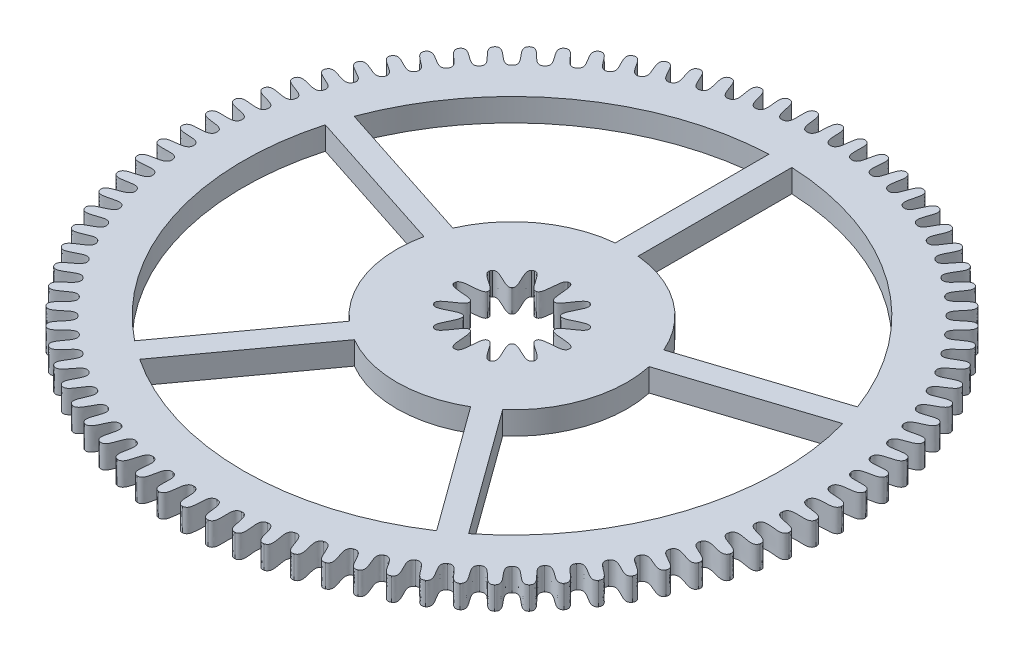
SolidWorks part; units mm, degrees
ref_plane "Alzado" through (0, 0, 0) normal (0, 0, 1) x (1, 0, 0)
ref_plane "Planta" through (0, 0, 0) normal (0, 1, 0) x (1, 0, 0)
ref_plane "Vista lateral" through (0, 0, 0) normal (1, 0, 0) x (0, 0, -1)
sketch "Sketch1" plane through (0, 0, 0) normal (0, 1, 0) x (1, 0, 0)
  line L0 (0, -1000) -> (0, 49000) construction
  line L1 (0, 0) -> (1869.5597, 49965.0352) construction
  circle A0 centre (0, 0) radius 4.315 construction
  circle A1 centre (0, 0) radius 4.015 construction
  spline S0 degree 3 poles (0, 4.315) (0.1353, 4.3129) (0.008, 4.0167) (0.1501, 4.0122) knots 0 0 0 0 1 1 1 1
  spline S1 degree 3 poles (0, 4.315) (-0.1353, 4.3129) (-0.008, 4.0167) (-0.1501, 4.0122) knots 0 0 0 0 1 1 1 1
  spline S2 degree 3 poles (0.3225, 4.3029) (0.4572, 4.2907) (0.3081, 4.0048) (0.4495, 3.9898) knots 0 0 0 0 1 1 1 1
  spline S3 degree 3 poles (0.3225, 4.3029) (0.1874, 4.3109) (0.2922, 4.006) (0.1501, 4.0122) knots 0 0 0 0 1 1 1 1
  spline S4 degree 3 poles (0.6431, 4.2668) (0.7765, 4.2445) (0.6066, 3.9706) (0.7464, 3.945) knots 0 0 0 0 1 1 1 1
  spline S5 degree 3 poles (0.6431, 4.2668) (0.5091, 4.2849) (0.5907, 3.973) (0.4495, 3.9898) knots 0 0 0 0 1 1 1 1
  spline S6 degree 3 poles (0.9602, 4.2068) (1.0916, 4.1746) (0.9016, 3.9142) (1.0392, 3.8782) knots 0 0 0 0 1 1 1 1
  spline S7 degree 3 poles (0.9602, 4.2068) (0.8278, 4.2348) (0.886, 3.9177) (0.7464, 3.945) knots 0 0 0 0 1 1 1 1
  spline S8 degree 3 poles (1.2719, 4.1233) (1.4005, 4.0814) (1.1916, 3.8358) (1.3261, 3.7897) knots 0 0 0 0 1 1 1 1
  spline S9 degree 3 poles (1.2719, 4.1233) (1.142, 4.1611) (1.1763, 3.8406) (1.0392, 3.8782) knots 0 0 0 0 1 1 1 1
  spline S10 degree 3 poles (1.5764, 4.0167) (1.7016, 3.9653) (1.4749, 3.7361) (1.6056, 3.68) knots 0 0 0 0 1 1 1 1
  spline S11 degree 3 poles (1.5764, 4.0167) (1.4498, 4.0642) (1.46, 3.7419) (1.3261, 3.7897) knots 0 0 0 0 1 1 1 1
  spline S12 degree 3 poles (1.8722, 3.8877) (1.9932, 3.8271) (1.75, 3.6154) (1.8761, 3.5497) knots 0 0 0 0 1 1 1 1
  spline S13 degree 3 poles (1.8722, 3.8877) (1.7494, 3.9445) (1.7356, 3.6223) (1.6056, 3.68) knots 0 0 0 0 1 1 1 1
  spline S14 degree 3 poles (2.1575, 3.7369) (2.2736, 3.6674) (2.0153, 3.4745) (2.1361, 3.3996) knots 0 0 0 0 1 1 1 1
  spline S15 degree 3 poles (2.1575, 3.7369) (2.0393, 3.8027) (2.0014, 3.4825) (1.8761, 3.5497) knots 0 0 0 0 1 1 1 1
  spline S16 degree 3 poles (2.4307, 3.5652) (2.5413, 3.4873) (2.2693, 3.3142) (2.3842, 3.2305) knots 0 0 0 0 1 1 1 1
  spline S17 degree 3 poles (2.4307, 3.5652) (2.3178, 3.6397) (2.2561, 3.3232) (2.1361, 3.3996) knots 0 0 0 0 1 1 1 1
  spline S18 degree 3 poles (2.6904, 3.3736) (2.7948, 3.2876) (2.5106, 3.1354) (2.6189, 3.0433) knots 0 0 0 0 1 1 1 1
  spline S19 degree 3 poles (2.6904, 3.3736) (2.5833, 3.4563) (2.4981, 3.1453) (2.3842, 3.2305) knots 0 0 0 0 1 1 1 1
  spline S20 degree 3 poles (2.9349, 3.1631) (3.0327, 3.0696) (2.7379, 2.939) (2.839, 2.839) knots 0 0 0 0 1 1 1 1
  spline S21 degree 3 poles (2.9349, 3.1631) (2.8344, 3.2536) (2.7262, 2.9499) (2.6189, 3.0433) knots 0 0 0 0 1 1 1 1
  spline S22 degree 3 poles (3.1631, 2.9349) (3.2536, 2.8344) (2.9499, 2.7262) (3.0433, 2.6189) knots 0 0 0 0 1 1 1 1
  spline S23 degree 3 poles (3.1631, 2.9349) (3.0696, 3.0327) (2.939, 2.7379) (2.839, 2.839) knots 0 0 0 0 1 1 1 1
  spline S24 degree 3 poles (3.3736, 2.6904) (3.4563, 2.5833) (3.1453, 2.4981) (3.2305, 2.3842) knots 0 0 0 0 1 1 1 1
  spline S25 degree 3 poles (3.3736, 2.6904) (3.2876, 2.7948) (3.1354, 2.5106) (3.0433, 2.6189) knots 0 0 0 0 1 1 1 1
  spline S26 degree 3 poles (3.5652, 2.4307) (3.6397, 2.3178) (3.3232, 2.2561) (3.3996, 2.1361) knots 0 0 0 0 1 1 1 1
  spline S27 degree 3 poles (3.5652, 2.4307) (3.4873, 2.5413) (3.3142, 2.2693) (3.2305, 2.3842) knots 0 0 0 0 1 1 1 1
  spline S28 degree 3 poles (3.7369, 2.1575) (3.8027, 2.0393) (3.4825, 2.0014) (3.5497, 1.8761) knots 0 0 0 0 1 1 1 1
  spline S29 degree 3 poles (3.7369, 2.1575) (3.6674, 2.2736) (3.4745, 2.0153) (3.3996, 2.1361) knots 0 0 0 0 1 1 1 1
  spline S30 degree 3 poles (3.8877, 1.8722) (3.9445, 1.7494) (3.6223, 1.7356) (3.68, 1.6056) knots 0 0 0 0 1 1 1 1
  spline S31 degree 3 poles (3.8877, 1.8722) (3.8271, 1.9932) (3.6154, 1.75) (3.5497, 1.8761) knots 0 0 0 0 1 1 1 1
  spline S32 degree 3 poles (4.0167, 1.5764) (4.0642, 1.4498) (3.7419, 1.46) (3.7897, 1.3261) knots 0 0 0 0 1 1 1 1
  spline S33 degree 3 poles (4.0167, 1.5764) (3.9653, 1.7016) (3.7361, 1.4749) (3.68, 1.6056) knots 0 0 0 0 1 1 1 1
  spline S34 degree 3 poles (4.1233, 1.2719) (4.1611, 1.142) (3.8406, 1.1763) (3.8782, 1.0392) knots 0 0 0 0 1 1 1 1
  spline S35 degree 3 poles (4.1233, 1.2719) (4.0814, 1.4005) (3.8358, 1.1916) (3.7897, 1.3261) knots 0 0 0 0 1 1 1 1
  spline S36 degree 3 poles (4.2068, 0.9602) (4.2348, 0.8278) (3.9177, 0.886) (3.945, 0.7464) knots 0 0 0 0 1 1 1 1
  spline S37 degree 3 poles (4.2068, 0.9602) (4.1746, 1.0916) (3.9142, 0.9016) (3.8782, 1.0392) knots 0 0 0 0 1 1 1 1
  spline S38 degree 3 poles (4.2668, 0.6431) (4.2849, 0.5091) (3.973, 0.5907) (3.9898, 0.4495) knots 0 0 0 0 1 1 1 1
  spline S39 degree 3 poles (4.2668, 0.6431) (4.2445, 0.7765) (3.9706, 0.6066) (3.945, 0.7464) knots 0 0 0 0 1 1 1 1
  spline S40 degree 3 poles (4.3029, 0.3225) (4.3109, 0.1874) (4.006, 0.2922) (4.0122, 0.1501) knots 0 0 0 0 1 1 1 1
  spline S41 degree 3 poles (4.3029, 0.3225) (4.2907, 0.4572) (4.0048, 0.3081) (3.9898, 0.4495) knots 0 0 0 0 1 1 1 1
  spline S42 degree 3 poles (4.315, 0) (4.3129, -0.1353) (4.0167, -0.008) (4.0122, -0.1501) knots 0 0 0 0 1 1 1 1
  spline S43 degree 3 poles (4.315, 0) (4.3129, 0.1353) (4.0167, 0.008) (4.0122, 0.1501) knots 0 0 0 0 1 1 1 1
  spline S44 degree 3 poles (4.3029, -0.3225) (4.2907, -0.4572) (4.0048, -0.3081) (3.9898, -0.4495) knots 0 0 0 0 1 1 1 1
  spline S45 degree 3 poles (4.3029, -0.3225) (4.3109, -0.1874) (4.006, -0.2922) (4.0122, -0.1501) knots 0 0 0 0 1 1 1 1
  spline S46 degree 3 poles (4.2668, -0.6431) (4.2445, -0.7765) (3.9706, -0.6066) (3.945, -0.7464) knots 0 0 0 0 1 1 1 1
  spline S47 degree 3 poles (4.2668, -0.6431) (4.2849, -0.5091) (3.973, -0.5907) (3.9898, -0.4495) knots 0 0 0 0 1 1 1 1
  spline S48 degree 3 poles (4.2068, -0.9602) (4.1746, -1.0916) (3.9142, -0.9016) (3.8782, -1.0392) knots 0 0 0 0 1 1 1 1
  spline S49 degree 3 poles (4.2068, -0.9602) (4.2348, -0.8278) (3.9177, -0.886) (3.945, -0.7464) knots 0 0 0 0 1 1 1 1
  spline S50 degree 3 poles (4.1233, -1.2719) (4.0814, -1.4005) (3.8358, -1.1916) (3.7897, -1.3261) knots 0 0 0 0 1 1 1 1
  spline S51 degree 3 poles (4.1233, -1.2719) (4.1611, -1.142) (3.8406, -1.1763) (3.8782, -1.0392) knots 0 0 0 0 1 1 1 1
  spline S52 degree 3 poles (4.0167, -1.5764) (3.9653, -1.7016) (3.7361, -1.4749) (3.68, -1.6056) knots 0 0 0 0 1 1 1 1
  spline S53 degree 3 poles (4.0167, -1.5764) (4.0642, -1.4498) (3.7419, -1.46) (3.7897, -1.3261) knots 0 0 0 0 1 1 1 1
  spline S54 degree 3 poles (3.8877, -1.8722) (3.8271, -1.9932) (3.6154, -1.75) (3.5497, -1.8761) knots 0 0 0 0 1 1 1 1
  spline S55 degree 3 poles (3.8877, -1.8722) (3.9445, -1.7494) (3.6223, -1.7356) (3.68, -1.6056) knots 0 0 0 0 1 1 1 1
  spline S56 degree 3 poles (3.7369, -2.1575) (3.6674, -2.2736) (3.4745, -2.0153) (3.3996, -2.1361) knots 0 0 0 0 1 1 1 1
  spline S57 degree 3 poles (3.7369, -2.1575) (3.8027, -2.0393) (3.4825, -2.0014) (3.5497, -1.8761) knots 0 0 0 0 1 1 1 1
  spline S58 degree 3 poles (3.5652, -2.4307) (3.4873, -2.5413) (3.3142, -2.2693) (3.2305, -2.3842) knots 0 0 0 0 1 1 1 1
  spline S59 degree 3 poles (3.5652, -2.4307) (3.6397, -2.3178) (3.3232, -2.2561) (3.3996, -2.1361) knots 0 0 0 0 1 1 1 1
  spline S60 degree 3 poles (3.3736, -2.6904) (3.2876, -2.7948) (3.1354, -2.5106) (3.0433, -2.6189) knots 0 0 0 0 1 1 1 1
  spline S61 degree 3 poles (3.3736, -2.6904) (3.4563, -2.5833) (3.1453, -2.4981) (3.2305, -2.3842) knots 0 0 0 0 1 1 1 1
  spline S62 degree 3 poles (3.1631, -2.9349) (3.0696, -3.0327) (2.939, -2.7379) (2.839, -2.839) knots 0 0 0 0 1 1 1 1
  spline S63 degree 3 poles (3.1631, -2.9349) (3.2536, -2.8344) (2.9499, -2.7262) (3.0433, -2.6189) knots 0 0 0 0 1 1 1 1
  spline S64 degree 3 poles (2.9349, -3.1631) (2.8344, -3.2536) (2.7262, -2.9499) (2.6189, -3.0433) knots 0 0 0 0 1 1 1 1
  spline S65 degree 3 poles (2.9349, -3.1631) (3.0327, -3.0696) (2.7379, -2.939) (2.839, -2.839) knots 0 0 0 0 1 1 1 1
  spline S66 degree 3 poles (2.6904, -3.3736) (2.5833, -3.4563) (2.4981, -3.1453) (2.3842, -3.2305) knots 0 0 0 0 1 1 1 1
  spline S67 degree 3 poles (2.6904, -3.3736) (2.7948, -3.2876) (2.5106, -3.1354) (2.6189, -3.0433) knots 0 0 0 0 1 1 1 1
  spline S68 degree 3 poles (2.4307, -3.5652) (2.3178, -3.6397) (2.2561, -3.3232) (2.1361, -3.3996) knots 0 0 0 0 1 1 1 1
  spline S69 degree 3 poles (2.4307, -3.5652) (2.5413, -3.4873) (2.2693, -3.3142) (2.3842, -3.2305) knots 0 0 0 0 1 1 1 1
  spline S70 degree 3 poles (2.1575, -3.7369) (2.0393, -3.8027) (2.0014, -3.4825) (1.8761, -3.5497) knots 0 0 0 0 1 1 1 1
  spline S71 degree 3 poles (2.1575, -3.7369) (2.2736, -3.6674) (2.0153, -3.4745) (2.1361, -3.3996) knots 0 0 0 0 1 1 1 1
  spline S72 degree 3 poles (1.8722, -3.8877) (1.7494, -3.9445) (1.7356, -3.6223) (1.6056, -3.68) knots 0 0 0 0 1 1 1 1
  spline S73 degree 3 poles (1.8722, -3.8877) (1.9932, -3.8271) (1.75, -3.6154) (1.8761, -3.5497) knots 0 0 0 0 1 1 1 1
  spline S74 degree 3 poles (1.5764, -4.0167) (1.4498, -4.0642) (1.46, -3.7419) (1.3261, -3.7897) knots 0 0 0 0 1 1 1 1
  spline S75 degree 3 poles (1.5764, -4.0167) (1.7016, -3.9653) (1.4749, -3.7361) (1.6056, -3.68) knots 0 0 0 0 1 1 1 1
  spline S76 degree 3 poles (1.2719, -4.1233) (1.142, -4.1611) (1.1763, -3.8406) (1.0392, -3.8782) knots 0 0 0 0 1 1 1 1
  spline S77 degree 3 poles (1.2719, -4.1233) (1.4005, -4.0814) (1.1916, -3.8358) (1.3261, -3.7897) knots 0 0 0 0 1 1 1 1
  spline S78 degree 3 poles (0.9602, -4.2068) (0.8278, -4.2348) (0.886, -3.9177) (0.7464, -3.945) knots 0 0 0 0 1 1 1 1
  spline S79 degree 3 poles (0.9602, -4.2068) (1.0916, -4.1746) (0.9016, -3.9142) (1.0392, -3.8782) knots 0 0 0 0 1 1 1 1
  spline S80 degree 3 poles (0.6431, -4.2668) (0.5091, -4.2849) (0.5907, -3.973) (0.4495, -3.9898) knots 0 0 0 0 1 1 1 1
  spline S81 degree 3 poles (0.6431, -4.2668) (0.7765, -4.2445) (0.6066, -3.9706) (0.7464, -3.945) knots 0 0 0 0 1 1 1 1
  spline S82 degree 3 poles (0.3225, -4.3029) (0.1874, -4.3109) (0.2922, -4.006) (0.1501, -4.0122) knots 0 0 0 0 1 1 1 1
  spline S83 degree 3 poles (0.3225, -4.3029) (0.4572, -4.2907) (0.3081, -4.0048) (0.4495, -3.9898) knots 0 0 0 0 1 1 1 1
  spline S84 degree 3 poles (0, -4.315) (-0.1353, -4.3129) (-0.008, -4.0167) (-0.1501, -4.0122) knots 0 0 0 0 1 1 1 1
  spline S85 degree 3 poles (0, -4.315) (0.1353, -4.3129) (0.008, -4.0167) (0.1501, -4.0122) knots 0 0 0 0 1 1 1 1
  spline S86 degree 3 poles (-0.3225, -4.3029) (-0.4572, -4.2907) (-0.3081, -4.0048) (-0.4495, -3.9898) knots 0 0 0 0 1 1 1 1
  spline S87 degree 3 poles (-0.3225, -4.3029) (-0.1874, -4.3109) (-0.2922, -4.006) (-0.1501, -4.0122) knots 0 0 0 0 1 1 1 1
  spline S88 degree 3 poles (-0.6431, -4.2668) (-0.7765, -4.2445) (-0.6066, -3.9706) (-0.7464, -3.945) knots 0 0 0 0 1 1 1 1
  spline S89 degree 3 poles (-0.6431, -4.2668) (-0.5091, -4.2849) (-0.5907, -3.973) (-0.4495, -3.9898) knots 0 0 0 0 1 1 1 1
  spline S90 degree 3 poles (-0.9602, -4.2068) (-1.0916, -4.1746) (-0.9016, -3.9142) (-1.0392, -3.8782) knots 0 0 0 0 1 1 1 1
  spline S91 degree 3 poles (-0.9602, -4.2068) (-0.8278, -4.2348) (-0.886, -3.9177) (-0.7464, -3.945) knots 0 0 0 0 1 1 1 1
  spline S92 degree 3 poles (-1.2719, -4.1233) (-1.4005, -4.0814) (-1.1916, -3.8358) (-1.3261, -3.7897) knots 0 0 0 0 1 1 1 1
  spline S93 degree 3 poles (-1.2719, -4.1233) (-1.142, -4.1611) (-1.1763, -3.8406) (-1.0392, -3.8782) knots 0 0 0 0 1 1 1 1
  spline S94 degree 3 poles (-1.5764, -4.0167) (-1.7016, -3.9653) (-1.4749, -3.7361) (-1.6056, -3.68) knots 0 0 0 0 1 1 1 1
  spline S95 degree 3 poles (-1.5764, -4.0167) (-1.4498, -4.0642) (-1.46, -3.7419) (-1.3261, -3.7897) knots 0 0 0 0 1 1 1 1
  spline S96 degree 3 poles (-1.8722, -3.8877) (-1.9932, -3.8271) (-1.75, -3.6154) (-1.8761, -3.5497) knots 0 0 0 0 1 1 1 1
  spline S97 degree 3 poles (-1.8722, -3.8877) (-1.7494, -3.9445) (-1.7356, -3.6223) (-1.6056, -3.68) knots 0 0 0 0 1 1 1 1
  spline S98 degree 3 poles (-2.1575, -3.7369) (-2.2736, -3.6674) (-2.0153, -3.4745) (-2.1361, -3.3996) knots 0 0 0 0 1 1 1 1
  spline S99 degree 3 poles (-2.1575, -3.7369) (-2.0393, -3.8027) (-2.0014, -3.4825) (-1.8761, -3.5497) knots 0 0 0 0 1 1 1 1
  spline S100 degree 3 poles (-2.4307, -3.5652) (-2.5413, -3.4873) (-2.2693, -3.3142) (-2.3842, -3.2305) knots 0 0 0 0 1 1 1 1
  spline S101 degree 3 poles (-2.4307, -3.5652) (-2.3178, -3.6397) (-2.2561, -3.3232) (-2.1361, -3.3996) knots 0 0 0 0 1 1 1 1
  spline S102 degree 3 poles (-2.6904, -3.3736) (-2.7948, -3.2876) (-2.5106, -3.1354) (-2.6189, -3.0433) knots 0 0 0 0 1 1 1 1
  spline S103 degree 3 poles (-2.6904, -3.3736) (-2.5833, -3.4563) (-2.4981, -3.1453) (-2.3842, -3.2305) knots 0 0 0 0 1 1 1 1
  spline S104 degree 3 poles (-2.9349, -3.1631) (-3.0327, -3.0696) (-2.7379, -2.939) (-2.839, -2.839) knots 0 0 0 0 1 1 1 1
  spline S105 degree 3 poles (-2.9349, -3.1631) (-2.8344, -3.2536) (-2.7262, -2.9499) (-2.6189, -3.0433) knots 0 0 0 0 1 1 1 1
  spline S106 degree 3 poles (-3.1631, -2.9349) (-3.2536, -2.8344) (-2.9499, -2.7262) (-3.0433, -2.6189) knots 0 0 0 0 1 1 1 1
  spline S107 degree 3 poles (-3.1631, -2.9349) (-3.0696, -3.0327) (-2.939, -2.7379) (-2.839, -2.839) knots 0 0 0 0 1 1 1 1
  spline S108 degree 3 poles (-3.3736, -2.6904) (-3.4563, -2.5833) (-3.1453, -2.4981) (-3.2305, -2.3842) knots 0 0 0 0 1 1 1 1
  spline S109 degree 3 poles (-3.3736, -2.6904) (-3.2876, -2.7948) (-3.1354, -2.5106) (-3.0433, -2.6189) knots 0 0 0 0 1 1 1 1
  spline S110 degree 3 poles (-3.5652, -2.4307) (-3.6397, -2.3178) (-3.3232, -2.2561) (-3.3996, -2.1361) knots 0 0 0 0 1 1 1 1
  spline S111 degree 3 poles (-3.5652, -2.4307) (-3.4873, -2.5413) (-3.3142, -2.2693) (-3.2305, -2.3842) knots 0 0 0 0 1 1 1 1
  spline S112 degree 3 poles (-3.7369, -2.1575) (-3.8027, -2.0393) (-3.4825, -2.0014) (-3.5497, -1.8761) knots 0 0 0 0 1 1 1 1
  spline S113 degree 3 poles (-3.7369, -2.1575) (-3.6674, -2.2736) (-3.4745, -2.0153) (-3.3996, -2.1361) knots 0 0 0 0 1 1 1 1
  spline S114 degree 3 poles (-3.8877, -1.8722) (-3.9445, -1.7494) (-3.6223, -1.7356) (-3.68, -1.6056) knots 0 0 0 0 1 1 1 1
  spline S115 degree 3 poles (-3.8877, -1.8722) (-3.8271, -1.9932) (-3.6154, -1.75) (-3.5497, -1.8761) knots 0 0 0 0 1 1 1 1
  spline S116 degree 3 poles (-4.0167, -1.5764) (-4.0642, -1.4498) (-3.7419, -1.46) (-3.7897, -1.3261) knots 0 0 0 0 1 1 1 1
  spline S117 degree 3 poles (-4.0167, -1.5764) (-3.9653, -1.7016) (-3.7361, -1.4749) (-3.68, -1.6056) knots 0 0 0 0 1 1 1 1
  spline S118 degree 3 poles (-4.1233, -1.2719) (-4.1611, -1.142) (-3.8406, -1.1763) (-3.8782, -1.0392) knots 0 0 0 0 1 1 1 1
  spline S119 degree 3 poles (-4.1233, -1.2719) (-4.0814, -1.4005) (-3.8358, -1.1916) (-3.7897, -1.3261) knots 0 0 0 0 1 1 1 1
  spline S120 degree 3 poles (-4.2068, -0.9602) (-4.2348, -0.8278) (-3.9177, -0.886) (-3.945, -0.7464) knots 0 0 0 0 1 1 1 1
  spline S121 degree 3 poles (-4.2068, -0.9602) (-4.1746, -1.0916) (-3.9142, -0.9016) (-3.8782, -1.0392) knots 0 0 0 0 1 1 1 1
  spline S122 degree 3 poles (-4.2668, -0.6431) (-4.2849, -0.5091) (-3.973, -0.5907) (-3.9898, -0.4495) knots 0 0 0 0 1 1 1 1
  spline S123 degree 3 poles (-4.2668, -0.6431) (-4.2445, -0.7765) (-3.9706, -0.6066) (-3.945, -0.7464) knots 0 0 0 0 1 1 1 1
  spline S124 degree 3 poles (-4.3029, -0.3225) (-4.3109, -0.1874) (-4.006, -0.2922) (-4.0122, -0.1501) knots 0 0 0 0 1 1 1 1
  spline S125 degree 3 poles (-4.3029, -0.3225) (-4.2907, -0.4572) (-4.0048, -0.3081) (-3.9898, -0.4495) knots 0 0 0 0 1 1 1 1
  spline S126 degree 3 poles (-4.315, 0) (-4.3129, 0.1353) (-4.0167, 0.008) (-4.0122, 0.1501) knots 0 0 0 0 1 1 1 1
  spline S127 degree 3 poles (-4.315, 0) (-4.3129, -0.1353) (-4.0167, -0.008) (-4.0122, -0.1501) knots 0 0 0 0 1 1 1 1
  spline S128 degree 3 poles (-4.3029, 0.3225) (-4.2907, 0.4572) (-4.0048, 0.3081) (-3.9898, 0.4495) knots 0 0 0 0 1 1 1 1
  spline S129 degree 3 poles (-4.3029, 0.3225) (-4.3109, 0.1874) (-4.006, 0.2922) (-4.0122, 0.1501) knots 0 0 0 0 1 1 1 1
  spline S130 degree 3 poles (-4.2668, 0.6431) (-4.2445, 0.7765) (-3.9706, 0.6066) (-3.945, 0.7464) knots 0 0 0 0 1 1 1 1
  spline S131 degree 3 poles (-4.2668, 0.6431) (-4.2849, 0.5091) (-3.973, 0.5907) (-3.9898, 0.4495) knots 0 0 0 0 1 1 1 1
  spline S132 degree 3 poles (-4.2068, 0.9602) (-4.1746, 1.0916) (-3.9142, 0.9016) (-3.8782, 1.0392) knots 0 0 0 0 1 1 1 1
  spline S133 degree 3 poles (-4.2068, 0.9602) (-4.2348, 0.8278) (-3.9177, 0.886) (-3.945, 0.7464) knots 0 0 0 0 1 1 1 1
  spline S134 degree 3 poles (-4.1233, 1.2719) (-4.0814, 1.4005) (-3.8358, 1.1916) (-3.7897, 1.3261) knots 0 0 0 0 1 1 1 1
  spline S135 degree 3 poles (-4.1233, 1.2719) (-4.1611, 1.142) (-3.8406, 1.1763) (-3.8782, 1.0392) knots 0 0 0 0 1 1 1 1
  spline S136 degree 3 poles (-4.0167, 1.5764) (-3.9653, 1.7016) (-3.7361, 1.4749) (-3.68, 1.6056) knots 0 0 0 0 1 1 1 1
  spline S137 degree 3 poles (-4.0167, 1.5764) (-4.0642, 1.4498) (-3.7419, 1.46) (-3.7897, 1.3261) knots 0 0 0 0 1 1 1 1
  spline S138 degree 3 poles (-3.8877, 1.8722) (-3.8271, 1.9932) (-3.6154, 1.75) (-3.5497, 1.8761) knots 0 0 0 0 1 1 1 1
  spline S139 degree 3 poles (-3.8877, 1.8722) (-3.9445, 1.7494) (-3.6223, 1.7356) (-3.68, 1.6056) knots 0 0 0 0 1 1 1 1
  spline S140 degree 3 poles (-3.7369, 2.1575) (-3.6674, 2.2736) (-3.4745, 2.0153) (-3.3996, 2.1361) knots 0 0 0 0 1 1 1 1
  spline S141 degree 3 poles (-3.7369, 2.1575) (-3.8027, 2.0393) (-3.4825, 2.0014) (-3.5497, 1.8761) knots 0 0 0 0 1 1 1 1
  spline S142 degree 3 poles (-3.5652, 2.4307) (-3.4873, 2.5413) (-3.3142, 2.2693) (-3.2305, 2.3842) knots 0 0 0 0 1 1 1 1
  spline S143 degree 3 poles (-3.5652, 2.4307) (-3.6397, 2.3178) (-3.3232, 2.2561) (-3.3996, 2.1361) knots 0 0 0 0 1 1 1 1
  spline S144 degree 3 poles (-3.3736, 2.6904) (-3.2876, 2.7948) (-3.1354, 2.5106) (-3.0433, 2.6189) knots 0 0 0 0 1 1 1 1
  spline S145 degree 3 poles (-3.3736, 2.6904) (-3.4563, 2.5833) (-3.1453, 2.4981) (-3.2305, 2.3842) knots 0 0 0 0 1 1 1 1
  spline S146 degree 3 poles (-3.1631, 2.9349) (-3.0696, 3.0327) (-2.939, 2.7379) (-2.839, 2.839) knots 0 0 0 0 1 1 1 1
  spline S147 degree 3 poles (-3.1631, 2.9349) (-3.2536, 2.8344) (-2.9499, 2.7262) (-3.0433, 2.6189) knots 0 0 0 0 1 1 1 1
  spline S148 degree 3 poles (-2.9349, 3.1631) (-2.8344, 3.2536) (-2.7262, 2.9499) (-2.6189, 3.0433) knots 0 0 0 0 1 1 1 1
  spline S149 degree 3 poles (-2.9349, 3.1631) (-3.0327, 3.0696) (-2.7379, 2.939) (-2.839, 2.839) knots 0 0 0 0 1 1 1 1
  spline S150 degree 3 poles (-2.6904, 3.3736) (-2.5833, 3.4563) (-2.4981, 3.1453) (-2.3842, 3.2305) knots 0 0 0 0 1 1 1 1
  spline S151 degree 3 poles (-2.6904, 3.3736) (-2.7948, 3.2876) (-2.5106, 3.1354) (-2.6189, 3.0433) knots 0 0 0 0 1 1 1 1
  spline S152 degree 3 poles (-2.4307, 3.5652) (-2.3178, 3.6397) (-2.2561, 3.3232) (-2.1361, 3.3996) knots 0 0 0 0 1 1 1 1
  spline S153 degree 3 poles (-2.4307, 3.5652) (-2.5413, 3.4873) (-2.2693, 3.3142) (-2.3842, 3.2305) knots 0 0 0 0 1 1 1 1
  spline S154 degree 3 poles (-2.1575, 3.7369) (-2.0393, 3.8027) (-2.0014, 3.4825) (-1.8761, 3.5497) knots 0 0 0 0 1 1 1 1
  spline S155 degree 3 poles (-2.1575, 3.7369) (-2.2736, 3.6674) (-2.0153, 3.4745) (-2.1361, 3.3996) knots 0 0 0 0 1 1 1 1
  spline S156 degree 3 poles (-1.8722, 3.8877) (-1.7494, 3.9445) (-1.7356, 3.6223) (-1.6056, 3.68) knots 0 0 0 0 1 1 1 1
  spline S157 degree 3 poles (-1.8722, 3.8877) (-1.9932, 3.8271) (-1.75, 3.6154) (-1.8761, 3.5497) knots 0 0 0 0 1 1 1 1
  spline S158 degree 3 poles (-1.5764, 4.0167) (-1.4498, 4.0642) (-1.46, 3.7419) (-1.3261, 3.7897) knots 0 0 0 0 1 1 1 1
  spline S159 degree 3 poles (-1.5764, 4.0167) (-1.7016, 3.9653) (-1.4749, 3.7361) (-1.6056, 3.68) knots 0 0 0 0 1 1 1 1
  spline S160 degree 3 poles (-1.2719, 4.1233) (-1.142, 4.1611) (-1.1763, 3.8406) (-1.0392, 3.8782) knots 0 0 0 0 1 1 1 1
  spline S161 degree 3 poles (-1.2719, 4.1233) (-1.4005, 4.0814) (-1.1916, 3.8358) (-1.3261, 3.7897) knots 0 0 0 0 1 1 1 1
  spline S162 degree 3 poles (-0.9602, 4.2068) (-0.8278, 4.2348) (-0.886, 3.9177) (-0.7464, 3.945) knots 0 0 0 0 1 1 1 1
  spline S163 degree 3 poles (-0.9602, 4.2068) (-1.0916, 4.1746) (-0.9016, 3.9142) (-1.0392, 3.8782) knots 0 0 0 0 1 1 1 1
  spline S164 degree 3 poles (-0.6431, 4.2668) (-0.5091, 4.2849) (-0.5907, 3.973) (-0.4495, 3.9898) knots 0 0 0 0 1 1 1 1
  spline S165 degree 3 poles (-0.6431, 4.2668) (-0.7765, 4.2445) (-0.6066, 3.9706) (-0.7464, 3.945) knots 0 0 0 0 1 1 1 1
  spline S166 degree 3 poles (-0.3225, 4.3029) (-0.1874, 4.3109) (-0.2922, 4.006) (-0.1501, 4.0122) knots 0 0 0 0 1 1 1 1
  spline S167 degree 3 poles (-0.3225, 4.3029) (-0.4572, 4.2907) (-0.3081, 4.0048) (-0.4495, 3.9898) knots 0 0 0 0 1 1 1 1
  point P4 (0, 4.315)
  point P9 (0.1501, 4.0122)
  point P264 (0, 0)
  point P267 (0, 0)
  dimension "D1" = 8.63
  dimension "D2" = 0.3
  dimension "D3" = 2.143
extrude "Boss-Extrude1 (84 teeth)" add sketch "Sketch1" along normal blind 0.3
sketch "Sketch2" plane through (0, 0, 0) normal (0, 1, 0) x (1, 0, 0)
  line L0 (0, -1000) -> (0, 49000) construction
  line L1 (0, 0) -> (12940.9523, 48296.2913) construction
  line L2 (0, 0.75) -> (0.015, 0.7499)
  line L3 (0, 0.75) -> (-0.015, 0.7499)
  line L4 (0.375, 0.6495) -> (0.3619, 0.6569)
  line L5 (0.375, 0.6495) -> (0.3879, 0.6419)
  line L6 (0.6495, 0.375) -> (0.6419, 0.3879)
  line L7 (0.6495, 0.375) -> (0.6569, 0.3619)
  line L8 (0.75, 0) -> (0.7499, 0.015)
  line L9 (0.75, 0) -> (0.7499, -0.015)
  line L10 (0.6495, -0.375) -> (0.6569, -0.3619)
  line L11 (0.6495, -0.375) -> (0.6419, -0.3879)
  line L12 (0.375, -0.6495) -> (0.3879, -0.6419)
  line L13 (0.375, -0.6495) -> (0.3619, -0.6569)
  line L14 (0, -0.75) -> (0.015, -0.7499)
  line L15 (0, -0.75) -> (-0.015, -0.7499)
  line L16 (-0.375, -0.6495) -> (-0.3619, -0.6569)
  line L17 (-0.375, -0.6495) -> (-0.3879, -0.6419)
  line L18 (-0.6495, -0.375) -> (-0.6419, -0.3879)
  line L19 (-0.6495, -0.375) -> (-0.6569, -0.3619)
  line L20 (-0.75, 0) -> (-0.7499, -0.015)
  line L21 (-0.75, 0) -> (-0.7498, 0.015)
  line L22 (-0.6495, 0.375) -> (-0.6569, 0.3619)
  line L23 (-0.6495, 0.375) -> (-0.6419, 0.3879)
  line L24 (-0.375, 0.6495) -> (-0.3879, 0.6419)
  line L25 (-0.375, 0.6495) -> (-0.3619, 0.6569)
  circle A0 centre (0, 0) radius 0.75 construction
  circle A1 centre (0, 0) radius 0.45 construction
  spline S0 degree 3 poles (0.015, 0.7499) (0.0898, 0.7265) (0.0375, 0.4506) (0.1165, 0.4347) knots 0 0 0 0 1 1 1 1
  spline S1 degree 3 poles (-0.015, 0.7499) (-0.0898, 0.7265) (-0.0375, 0.4506) (-0.1165, 0.4347) knots 0 0 0 0 1 1 1 1
  spline S2 degree 3 poles (0.3619, 0.6569) (0.2767, 0.6794) (0.1928, 0.409) (0.1165, 0.4347) knots 0 0 0 0 1 1 1 1
  spline S3 degree 3 poles (0.3879, 0.6419) (0.4501, 0.5793) (0.2578, 0.3714) (0.3182, 0.3182) knots 0 0 0 0 1 1 1 1
  spline S4 degree 3 poles (0.6419, 0.3879) (0.5793, 0.4501) (0.3714, 0.2578) (0.3182, 0.3182) knots 0 0 0 0 1 1 1 1
  spline S5 degree 3 poles (0.6569, 0.3619) (0.6794, 0.2767) (0.409, 0.1928) (0.4347, 0.1165) knots 0 0 0 0 1 1 1 1
  spline S6 degree 3 poles (0.7499, 0.015) (0.7268, 0.1001) (0.4506, 0.0375) (0.4347, 0.1165) knots 0 0 0 0 1 1 1 1
  spline S7 degree 3 poles (0.7499, -0.015) (0.7268, -0.1001) (0.4506, -0.0375) (0.4347, -0.1165) knots 0 0 0 0 1 1 1 1
  spline S8 degree 3 poles (0.6569, -0.3619) (0.6794, -0.2767) (0.409, -0.1928) (0.4347, -0.1165) knots 0 0 0 0 1 1 1 1
  spline S9 degree 3 poles (0.6419, -0.3879) (0.5793, -0.4501) (0.3714, -0.2578) (0.3182, -0.3182) knots 0 0 0 0 1 1 1 1
  spline S10 degree 3 poles (0.3879, -0.6419) (0.4501, -0.5793) (0.2578, -0.3714) (0.3182, -0.3182) knots 0 0 0 0 1 1 1 1
  spline S11 degree 3 poles (0.3619, -0.6569) (0.2767, -0.6794) (0.1928, -0.409) (0.1165, -0.4347) knots 0 0 0 0 1 1 1 1
  spline S12 degree 3 poles (0.015, -0.7498) (0.1001, -0.7268) (0.0375, -0.4506) (0.1165, -0.4347) knots 0 0 0 0 1 1 1 1
  spline S13 degree 3 poles (-0.015, -0.7498) (-0.1001, -0.7268) (-0.0375, -0.4506) (-0.1165, -0.4347) knots 0 0 0 0 1 1 1 1
  spline S14 degree 3 poles (-0.3619, -0.6569) (-0.2767, -0.6794) (-0.1928, -0.409) (-0.1165, -0.4347) knots 0 0 0 0 1 1 1 1
  spline S15 degree 3 poles (-0.3879, -0.6419) (-0.4501, -0.5793) (-0.2578, -0.3714) (-0.3182, -0.3182) knots 0 0 0 0 1 1 1 1
  spline S16 degree 3 poles (-0.6419, -0.3879) (-0.5793, -0.4501) (-0.3714, -0.2578) (-0.3182, -0.3182) knots 0 0 0 0 1 1 1 1
  spline S17 degree 3 poles (-0.6569, -0.3619) (-0.6794, -0.2767) (-0.409, -0.1928) (-0.4347, -0.1165) knots 0 0 0 0 1 1 1 1
  spline S18 degree 3 poles (-0.7498, -0.015) (-0.7268, -0.1001) (-0.4506, -0.0375) (-0.4347, -0.1165) knots 0 0 0 0 1 1 1 1
  spline S19 degree 3 poles (-0.7498, 0.015) (-0.7268, 0.1001) (-0.4506, 0.0375) (-0.4347, 0.1165) knots 0 0 0 0 1 1 1 1
  spline S20 degree 3 poles (-0.6569, 0.3619) (-0.6794, 0.2767) (-0.409, 0.1928) (-0.4347, 0.1165) knots 0 0 0 0 1 1 1 1
  spline S21 degree 3 poles (-0.6419, 0.3879) (-0.5793, 0.4501) (-0.3714, 0.2578) (-0.3182, 0.3182) knots 0 0 0 0 1 1 1 1
  spline S22 degree 3 poles (-0.3879, 0.6419) (-0.4501, 0.5793) (-0.2578, 0.3714) (-0.3182, 0.3182) knots 0 0 0 0 1 1 1 1
  spline S23 degree 3 poles (-0.3619, 0.6569) (-0.2767, 0.6794) (-0.1928, 0.409) (-0.1165, 0.4347) knots 0 0 0 0 1 1 1 1
  point P4 (0.015, 0.7499)
  point P9 (0, 0.75)
  point P10 (0.1165, 0.4347)
  point P74 (0, 0)
  dimension "D1" = 1.5
  dimension "D2" = 0.9
  dimension "D3" = 15
  dimension "D4" = 0.015
  dimension "D5" = 12
extrude "Cut-Extrude1" cut sketch "Sketch2" along normal blind 0.3
sketch "Sketch3" plane through (0, 0, 0) normal (0, 1, 0) x (1, 0, 0)
  line L0 (0, -1000) -> (0, 49000) construction
  line L1 (0.15, -999.8847) -> (0.15, 49000.1153) construction
  line L2 (-0.15, -999.6818) -> (-0.15, 49000.3182) construction
  line L3 (-0.15, 3.5118) -> (-0.15, 1.5005)
  line L4 (3.2936, 1.2279) -> (1.3807, 0.6063)
  line L5 (0.15, 1.5005) -> (0.15, 3.5118)
  line L6 (1.4734, 0.321) -> (3.3863, 0.9425)
  line L7 (2.1855, -2.7529) -> (1.0033, -1.1258)
  line L8 (0.7606, -1.3021) -> (1.9428, -2.9293)
  line L9 (-1.9428, -2.9293) -> (-0.7606, -1.3021)
  line L10 (-1.0033, -1.1258) -> (-2.1855, -2.7529)
  line L11 (-3.3863, 0.9425) -> (-1.4734, 0.321)
  line L12 (-1.3807, 0.6063) -> (-3.2936, 1.2279)
  arc A0 (-0.15, 3.5118) -> (-3.2936, 1.2279) centre (0, 0) ccw
  arc A1 (-0.15, 1.5005) -> (-1.3807, 0.6063) centre (0, 0) ccw
  arc A2 (-3.3863, 0.9425) -> (-2.1855, -2.7529) centre (0, 0) ccw
  arc A3 (-1.4734, 0.321) -> (-1.0033, -1.1258) centre (0, 0) ccw
  arc A4 (1.3807, 0.6063) -> (0.15, 1.5005) centre (0, 0) ccw
  arc A5 (3.2936, 1.2279) -> (0.15, 3.5118) centre (0, 0) ccw
  arc A6 (1.0033, -1.1258) -> (1.4734, 0.321) centre (0, 0) ccw
  arc A7 (-0.7606, -1.3021) -> (0.7606, -1.3021) centre (0, 0) ccw
  arc A8 (-1.9428, -2.9293) -> (1.9428, -2.9293) centre (0, 0) ccw
  arc A9 (2.1855, -2.7529) -> (3.3863, 0.9425) centre (0, 0) ccw
  point P32 (0, 0)
  dimension "D3" = 7.03
  dimension "D4" = 3.016
  dimension "D1" = 0.15
  dimension "D2" = 0.15
  dimension "D5" = 5
extrude "Cut-Extrude2" cut sketch "Sketch3" along normal up to next
